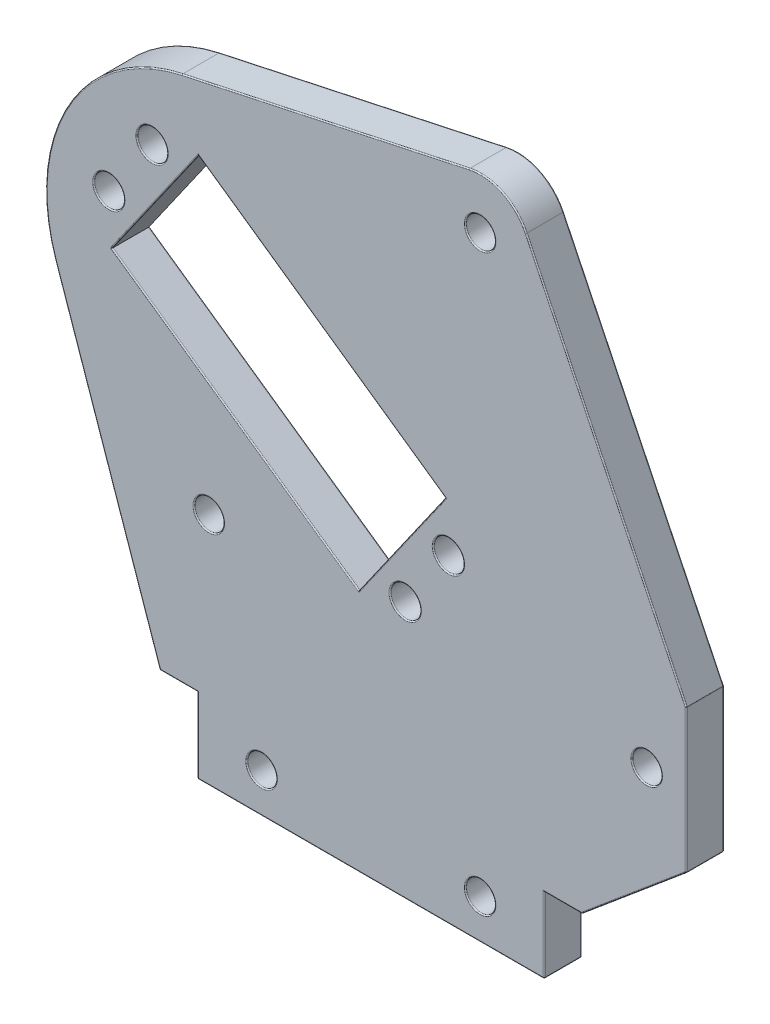
SolidWorks part; units mm, degrees
ref_plane "Front Plane" through (0, 0, 0) normal (0, 0, 1) x (1, 0, 0)
ref_plane "Top Plane" through (0, 0, 0) normal (0, 1, 0) x (1, 0, 0)
ref_plane "Right Plane" through (0, 0, 0) normal (1, 0, 0) x (0, 0, -1)
sketch "Sketch2" plane through (0, 0, 0) normal (0, 0, 1) x (1, 0, 0)
  line L0 (-23, 0) -> (-23, 10) construction
  line L1 (-23, 10) -> (-28, 10) construction
  line L2 (-28, 10) -> (-41.8438, 50.1182) construction
  line L3 (-25.0297, 79.9436) -> (13.0723, 88.1382) construction
  line L4 (41.85, 40.6215) -> (20.6106, 84.4605) construction
  line L5 (41.85, 21.6215) -> (41.85, 40.6215) construction
  line L6 (28, 10) -> (41.85, 21.6215) construction
  line L7 (23, 10) -> (28, 10) construction
  line L8 (-23, 0) -> (23, 0) construction
  line L9 (23, 0) -> (23, 10) construction
  line L10 (-23, 0) -> (-23, 10)
  line L11 (-23, 10) -> (-28, 10)
  line L12 (-28, 10) -> (-41.8438, 50.1182)
  line L13 (-25.0297, 79.9436) -> (13.0723, 88.1382)
  line L14 (41.85, 40.6215) -> (20.6106, 84.4605)
  line L15 (41.85, 21.6215) -> (41.85, 40.6215)
  line L16 (28, 10) -> (41.85, 21.6215)
  line L17 (23, 10) -> (28, 10)
  line L18 (-23, 0) -> (23, 0)
  line L19 (23, 0) -> (23, 10)
  line L20 (0, 0) -> (0, 10) construction
  line L21 (-22.8805, 71.6507) -> (-34.3521, 55.2676)
  line L22 (-22.8805, 71.6507) -> (9.8855, 48.7076)
  line L23 (-34.3521, 55.2676) -> (-1.586, 32.3246)
  line L24 (9.8855, 48.7076) -> (-1.586, 32.3246)
  line L25 (4.1498, 40.5161) -> (-28.6163, 63.4592) construction
  line L26 (-22.8805, 71.6507) -> (-34.3521, 55.2676) construction
  line L30 (-28.6163, 63.4592) -> (-33.5312, 66.9006) construction
  line L31 (-33.5312, 66.9006) -> (-28.6163, 63.4592) construction
  line L32 (-33.5312, 66.9006) -> (-27.7955, 75.0921) construction
  line L33 (-28.6163, 63.4592) -> (-22.8805, 71.6507) construction
  line L34 (-27.7955, 75.0921) -> (-22.8805, 71.6507) construction
  line L39 (-33.5312, 66.9006) -> (-28.6163, 63.4592) construction
  line L40 (-33.5312, 66.9006) -> (-39.267, 58.7091) construction
  line L41 (-28.6163, 63.4592) -> (-34.3521, 55.2676) construction
  line L42 (-39.267, 58.7091) -> (-34.3521, 55.2676) construction
  line L43 (-30.6633, 70.9964) -> (-25.7484, 67.5549) construction
  line L44 (-36.3991, 62.8049) -> (-31.4842, 59.3634) construction
  line L45 (-17.969, 43.7961) -> (-6.4975, 60.1792) construction
  arc A0 (-25.0297, 79.9436) -> (-41.8438, 50.1182) centre (-20.22, 57.58) ccw construction
  arc A1 (20.6106, 84.4605) -> (13.0723, 88.1382) centre (14.5, 81.5) ccw construction
  arc A2 (-25.0297, 79.9436) -> (-41.8438, 50.1182) centre (-20.22, 57.58) ccw
  arc A3 (20.6106, 84.4605) -> (13.0723, 88.1382) centre (14.5, 81.5) ccw
  circle A6 centre (-29.025, 69.8492) radius 2
  circle A7 centre (-34.7608, 61.6577) radius 2
  circle A8 centre (10.2943, 42.3176) radius 2
  circle A9 centre (4.5585, 34.126) radius 2
  circle A10 centre (14.5, 81.5) radius 1.95
  circle A11 centre (36.6, 31.1215) radius 1.95
  circle A12 centre (14.5, 5.25) radius 1.95
  circle A13 centre (-14.5, 5.25) radius 1.95
  circle A14 centre (-21.5, 31.1215) radius 1.95
  point P2 (-14.5, 5.25)
  point P4 (14.5, 5.25)
  point P8 (36.6, 31.1215)
  point P9 (-21.5, 31.1215)
  point P13 (41.85, 31.1215)
  point P15 (14.5, 81.5)
  point P26 (-20.22, 57.58)
  dimension "D9" = 4
  dimension "D10" = 3.9
  dimension "D1" = 5.25
  dimension "D2" = 5.25
  dimension "D3" = 21.5
  dimension "D4" = 40
  dimension "D5" = 20
  dimension "D6" = 35
  dimension "D7" = 10.25
  dimension "D8" = 6
extrude "Boss-Extrude2" add sketch "Sketch2" against normal blind 5
fillet "Fillet1" radius 0.15 56 edges at (-19.55, 31.1215, 0) (-19.55, 31.1215, -5) (-12.55, 5.25, 0) (-12.55, 5.25, -5) (16.45, 5.25, 0) (16.45, 5.25, -5) (38.55, 31.1215, 0) (38.55, 31.1215, -5) (16.45, 81.5, 0) (16.45, 81.5, -5) (6.5585, 34.126, 0) (6.5585, 34.126, -5) (8.2943, 42.3176, 0) (8.2943, 42.3176, -5) (-36.7608, 61.6577, 0) (-36.7608, 61.6577, -5) (-27.025, 69.8492, 0) (-27.025, 69.8492, -5) (-6.4975, 60.1792, 0) (-28.6163, 63.4592, 0) (-17.969, 43.7961, 0) (4.1498, 40.5161, 0) (-6.4975, 60.1792, -5) (-28.6163, 63.4592, -5) (-17.969, 43.7961, -5) (4.1498, 40.5161, -5) (0, 0, 0) (23, 5, 0) (25.5, 10, 0) (34.925, 15.8108, 0) (41.85, 31.1215, 0) (31.2303, 62.541, 0) (17.4772, 87.6025, 0) (-5.9787, 84.0409, 0) (-40.1467, 68.8136, 0) (-34.9219, 30.0591, 0) (-25.5, 10, 0) (-23, 5, 0) (0, 0, -5) (23, 5, -5) (25.5, 10, -5) (34.925, 15.8108, -5) (41.85, 31.1215, -5) (31.2303, 62.541, -5) (17.4772, 87.6025, -5) (-5.9787, 84.0409, -5) (-40.1467, 68.8136, -5) (-34.9219, 30.0591, -5) (-25.5, 10, -5) (-23, 5, -5) (28, 10, -2.5) (41.85, 21.6215, -2.5) (41.85, 40.6215, -2.5) (-28, 10, -2.5) (-23, 0, -2.5) (23, 0, -2.5)
